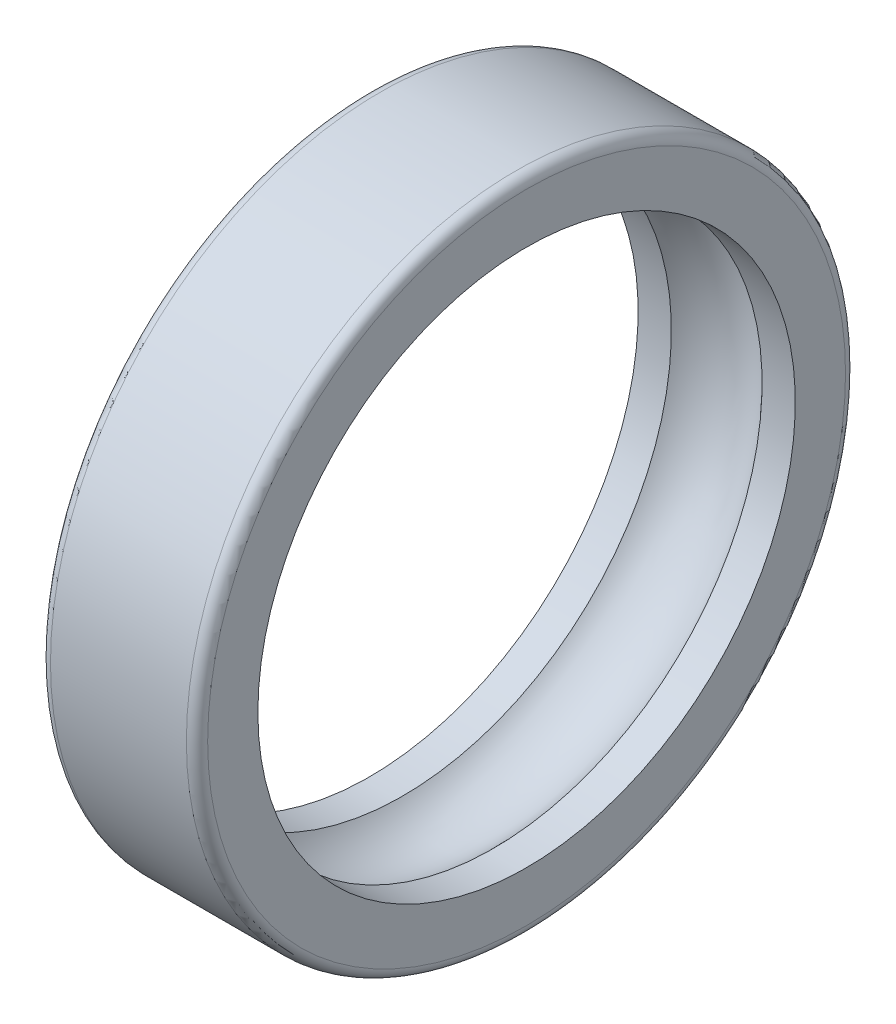
SolidWorks part; units mm, degrees
material "Cast Stainless Steel"
ref_plane "Front Plane" through (0, 0, 0) normal (0, 0, 1) x (1, 0, 0)
ref_plane "Top Plane" through (0, 0, 0) normal (0, 1, 0) x (1, 0, 0)
ref_plane "Right Plane" through (0, 0, 0) normal (1, 0, 0) x (0, 0, -1)
sketch "Sketch1" plane through (0, 0, 0) normal (0, 0, 1) x (1, 0, 0)
  line L0 (-41.5277, 0) -> (71.5047, 0) construction
  line L1 (-96.8064, 0) -> (-41.5277, 0) construction
  line L2 (-15.5, 65) -> (15.5, 65)
  line L3 (-15.5, 65) -> (-15.5, 53)
  line L4 (-15.5, 53) -> (-8.9443, 53)
  line L5 (15.5, 65) -> (15.5, 53)
  line L6 (-15.5, 65) -> (15.5, 53) construction
  line L7 (-15.5, 53) -> (15.5, 65) construction
  line L8 (0, 57) -> (0, 90.5848) construction
  line L9 (8.9443, 53) -> (15.5, 53)
  line L10 (0, 0) -> (0, 50.2958) construction
  arc A0 (8.9443, 53) -> (-8.9443, 53) centre (0, 45) ccw
  point P3 (0, 59)
  dimension "D5" = 12
  dimension "D1" = 31
  dimension "D2" = 53
  dimension "D3" = 65
  dimension "D4" = 8
revolve "Revolve1" add sketch "Sketch1" angle 360 about L0
fillet "Fillet1" radius 2.1 2 edges at (15.5, 0, 65) (-15.5, 0, 65)
